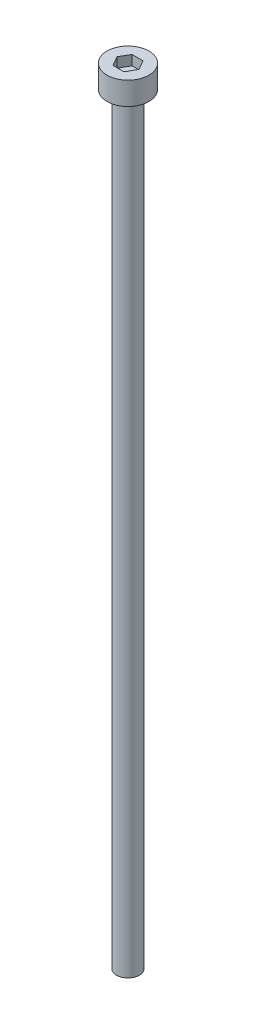
SolidWorks part; units mm, degrees
material "AISI 304"
ref_plane "前视基准面" through (0, 0, 0) normal (0, 0, 1) x (1, 0, 0)
ref_plane "上视基准面" through (0, 0, 0) normal (0, 1, 0) x (1, 0, 0)
ref_plane "右视基准面" through (0, 0, 0) normal (1, 0, 0) x (0, 0, -1)
sketch "草图1" plane through (0, 0, 0) normal (0, 1, 0) x (1, 0, 0)
  circle A0 centre (0, 0) radius 2.75
  dimension "D1" = 5.5
extrude "杯头" add sketch "草图1" along normal blind 3
sketch "草图2" plane through (0, 3, 0) normal (0, 1, 0) x (1, 0, 0)
  line L1 (1.4434, 0) -> (0.7217, 1.25)
  line L2 (0.7217, 1.25) -> (-0.7217, 1.25)
  line L3 (-0.7217, 1.25) -> (-1.4434, 0)
  line L4 (-1.4434, 0) -> (-0.7217, -1.25)
  line L5 (-0.7217, -1.25) -> (0.7217, -1.25)
  line L6 (0.7217, -1.25) -> (1.4434, 0)
  circle A0 centre (0, 0) radius 1.25 construction
  dimension "D1" = 2.5
extrude "内六角口" cut sketch "草图2" against normal blind 1.3
sketch "草图3" plane through (0, 0, 0) normal (0, -1, 0) x (1, 0, 0)
  circle A0 centre (0, 0) radius 1.5
  dimension "D1" = 3
extrude "螺纹长" add sketch "草图3" along normal blind 100
